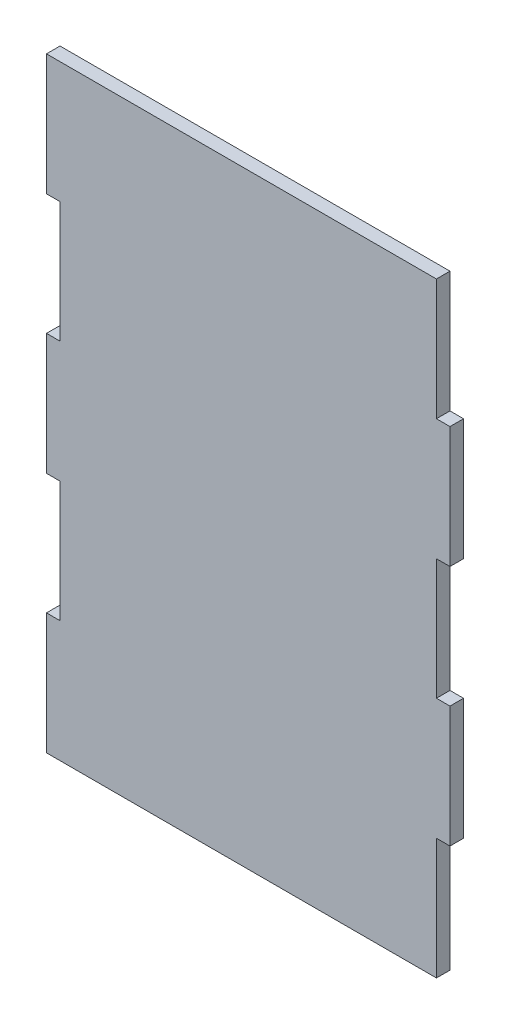
SolidWorks part; units mm, degrees
ref_plane "Front Plane" through (0, 0, 0) normal (0, 0, 1) x (1, 0, 0)
ref_plane "Top Plane" through (0, 0, 0) normal (0, 1, 0) x (1, 0, 0)
ref_plane "Right Plane" through (0, 0, 0) normal (1, 0, 0) x (0, 0, -1)
sketch "Sketch1" plane through (0, 0, 0) normal (0, 0, 1) x (1, 0, 0)
  line L1 (-75.0125, -120.6625) -> (75.0125, -120.6625)
  line L2 (-75.0125, -120.6625) -> (-75.0125, 120.6625)
  line L3 (-75.0125, 120.6625) -> (75.0125, 120.6625)
  line L4 (75.0125, -120.6625) -> (75.0125, 120.6625)
  line L5 (-75.0125, -120.6625) -> (75.0125, 120.6625) construction
  line L6 (-75.0125, 120.6625) -> (75.0125, -120.6625) construction
  line L7 (75.0125, -72.3975) -> (80.4125, -72.3975)
  line L8 (75.0125, -72.3975) -> (75.0125, -24.1325)
  line L9 (75.0125, -24.1325) -> (80.4125, -24.1325)
  line L10 (80.4125, -72.3975) -> (80.4125, -24.1325)
  line L11 (75.0125, 24.1325) -> (80.4125, 24.1325)
  line L12 (75.0125, 24.1325) -> (75.0125, 72.3975)
  line L13 (75.0125, 72.3975) -> (80.4125, 72.3975)
  line L14 (80.4125, 24.1325) -> (80.4125, 72.3975)
  line L15 (-75.0125, -120.6625) -> (-80.4125, -120.6625)
  line L16 (-75.0125, -120.6625) -> (-75.0125, -72.3975)
  line L17 (-75.0125, -72.3975) -> (-80.4125, -72.3975)
  line L18 (-80.4125, -120.6625) -> (-80.4125, -72.3975)
  line L19 (-75.0125, -24.1325) -> (-80.4125, -24.1325)
  line L20 (-75.0125, -24.1325) -> (-75.0125, 24.1325)
  line L21 (-75.0125, 24.1325) -> (-80.4125, 24.1325)
  line L22 (-80.4125, -24.1325) -> (-80.4125, 24.1325)
  line L23 (-75.0125, 72.3975) -> (-80.4125, 72.3975)
  line L24 (-75.0125, 72.3975) -> (-75.0125, 120.6625)
  line L25 (-75.0125, 120.6625) -> (-80.4125, 120.6625)
  line L26 (-80.4125, 72.3975) -> (-80.4125, 120.6625)
  line L27 (75.0125, 120.6625) -> (55.5875, 120.6625)
  point P0 (0, 0)
  dimension "D1" = 241.325
  dimension "D2" = 150.025
  dimension "D3" = 5.4
  dimension "D4" = 48.265
  dimension "D5" = 48.265
  dimension "D6" = 5.4
  dimension "D7" = 48.265
  dimension "D8" = 48.265
  dimension "D9" = 5.4
  dimension "D10" = 5.4
  dimension "D11" = 5.4
  dimension "D12" = 48.265
  dimension "D13" = 48.265
extrude "Boss-Extrude1" add sketch "Sketch1" along normal blind 5.4
sketch "Sketch2" plane through (0, 0, 5.4) normal (0, 0, 1) x (1, 0, 0)
  line L40 (-80.4531, -120.7031) -> (75.0531, -120.7031)
  line L41 (75.0531, -120.7031) -> (75.0531, -72.4381)
  line L42 (75.0531, -72.4381) -> (80.4531, -72.4381)
  line L43 (80.4531, -72.4381) -> (80.4531, -24.0919)
  line L44 (80.4531, -24.0919) -> (75.0531, -24.0919)
  line L45 (75.0531, -24.0919) -> (75.0531, 24.0919)
  line L46 (75.0531, 24.0919) -> (80.4531, 24.0919)
  line L47 (80.4531, 24.0919) -> (80.4531, 72.4381)
  line L48 (80.4531, 72.4381) -> (75.0531, 72.4381)
  line L49 (75.0531, 72.4381) -> (75.0531, 120.7031)
  line L50 (75.0531, 120.7031) -> (-80.4531, 120.7031)
  line L51 (-80.4531, 120.7031) -> (-80.4531, 72.3569)
  line L52 (-80.4531, 72.3569) -> (-75.0531, 72.3569)
  line L53 (-75.0531, 72.3569) -> (-75.0531, 24.1731)
  line L54 (-75.0531, 24.1731) -> (-80.4531, 24.1731)
  line L55 (-80.4531, 24.1731) -> (-80.4531, -24.1731)
  line L56 (-80.4531, -24.1731) -> (-75.0531, -24.1731)
  line L57 (-75.0531, -24.1731) -> (-75.0531, -72.3569)
  line L58 (-75.0531, -72.3569) -> (-80.4531, -72.3569)
  line L59 (-80.4531, -72.3569) -> (-80.4531, -120.7031)
  line L60 (-80.4531, -120.7031) -> (75.0531, -120.7031)
  line L61 (75.0531, -120.7031) -> (75.0531, -72.4381)
  line L62 (75.0531, -72.4381) -> (80.4531, -72.4381)
  line L63 (80.4531, -72.4381) -> (80.4531, -24.0919)
  line L64 (80.4531, -24.0919) -> (75.0531, -24.0919)
  line L65 (75.0531, -24.0919) -> (75.0531, 24.0919)
  line L66 (75.0531, 24.0919) -> (80.4531, 24.0919)
  line L67 (80.4531, 24.0919) -> (80.4531, 72.4381)
  line L68 (80.4531, 72.4381) -> (75.0531, 72.4381)
  line L69 (75.0531, 72.4381) -> (75.0531, 120.7031)
  line L70 (75.0531, 120.7031) -> (-80.4531, 120.7031)
  line L71 (-80.4531, 120.7031) -> (-80.4531, 72.3569)
  line L72 (-80.4531, 72.3569) -> (-75.0531, 72.3569)
  line L73 (-75.0531, 72.3569) -> (-75.0531, 24.1731)
  line L74 (-75.0531, 24.1731) -> (-80.4531, 24.1731)
  line L75 (-80.4531, 24.1731) -> (-80.4531, -24.1731)
  line L76 (-80.4531, -24.1731) -> (-75.0531, -24.1731)
  line L77 (-75.0531, -24.1731) -> (-75.0531, -72.3569)
  line L78 (-75.0531, -72.3569) -> (-80.4531, -72.3569)
  line L79 (-80.4531, -72.3569) -> (-80.4531, -120.7031)
  dimension "D1" = 0.0406
extrude "Boss-Extrude2" add sketch "Sketch2" against normal up to surface (5.4 mm away) up to face at (-0.54, 0, 0)
